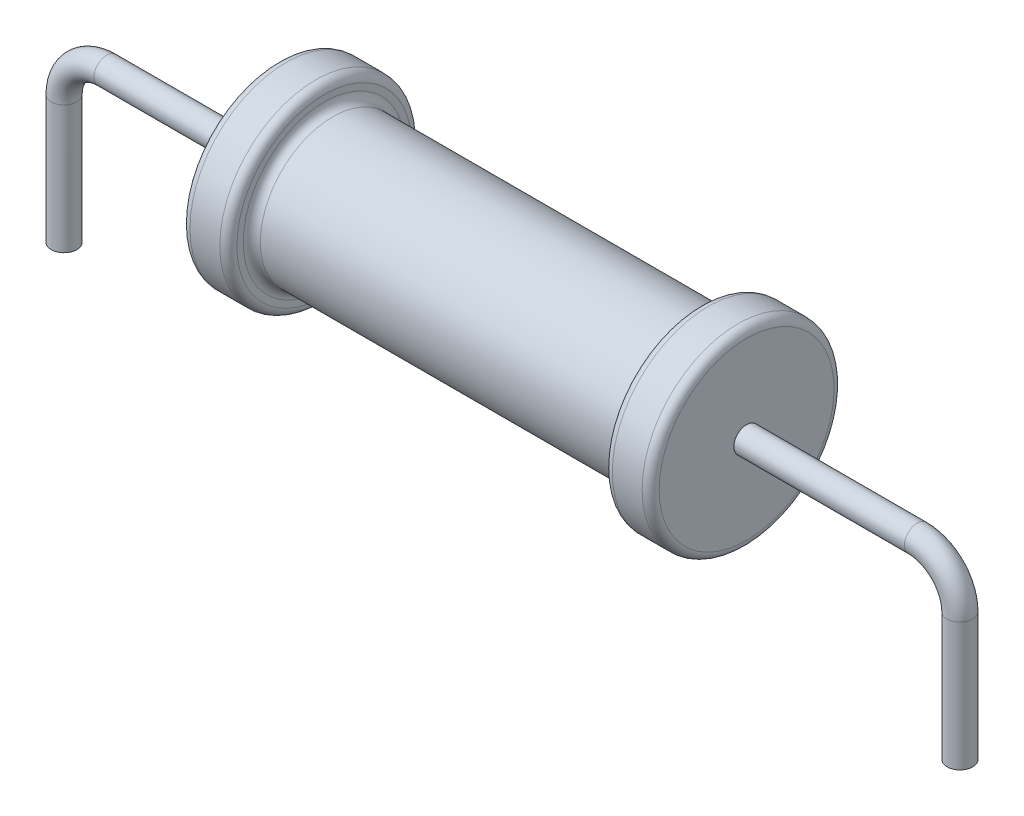
SolidWorks part; units mm, degrees
ref_plane "Спереди" through (0, 0, 0) normal (0, 0, 1) x (1, 0, 0)
ref_plane "Сверху" through (0, 0, 0) normal (0, 1, 0) x (1, 0, 0)
ref_plane "Справа" through (0, 0, 0) normal (1, 0, 0) x (0, 0, -1)
sketch "Эскиз2" plane through (0, 0, 0) normal (0, 1, 0) x (1, 0, 0)
  line L0 (-5.422, 0) -> (5.578, 0)
  line L1 (5.578, 0) -> (5.578, 2.05)
  line L2 (5.378, 2.25) -> (4.678, 2.25)
  line L3 (4.478, 2.05) -> (4.478, 1.9)
  line L4 (4.278, 1.7) -> (-4.122, 1.7)
  line L5 (-4.322, 1.9) -> (-4.322, 2.05)
  line L6 (-4.522, 2.25) -> (-5.222, 2.25)
  line L7 (-5.422, 2.05) -> (-5.422, 0)
  arc A0 (-5.222, 2.25) -> (-5.422, 2.05) centre (-5.222, 2.05) ccw
  arc A1 (4.278, 1.7) -> (4.478, 1.9) centre (4.278, 1.9) ccw
  arc A2 (5.578, 2.05) -> (5.378, 2.25) centre (5.378, 2.05) ccw
  arc A3 (4.678, 2.25) -> (4.478, 2.05) centre (4.678, 2.05) ccw
  arc A4 (-4.322, 1.9) -> (-4.122, 1.7) centre (-4.122, 1.9) ccw
  arc A5 (-4.322, 2.05) -> (-4.522, 2.25) centre (-4.522, 2.05) ccw
  point P11 (-5.422, 2.25)
  point P14 (4.478, 1.7)
  point P17 (5.578, 2.25)
  point P20 (4.478, 2.25)
  point P23 (-4.322, 1.7)
  point P26 (-4.322, 2.25)
  dimension "D7" = 0.2
  dimension "D8" = 0.2
  dimension "D1" = 11
  dimension "D2" = 1.1
  dimension "D3" = 1.1
  dimension "D4" = 0.55
  dimension "D5" = 0.55
  dimension "D6" = 2.25
revolve "Повернуть7" add sketch "Эскиз2" angle 360 about L0
sketch "Эскиз47" plane through (0, 0, 0) normal (0, 0, 1) x (1, 0, 0)
  line L0 (-5.422, 0) -> (-9.422, 0)
  line L1 (-5.422, 2.05) -> (-5.422, -2.05) construction
  line L2 (-10.422, -1) -> (-10.422, -4)
  arc A1 (-9.422, 0) -> (-10.422, -1) centre (-9.422, -1) ccw
  point P16 (-10.422, 0)
  dimension "D1" = 4
  dimension "D2" = 5
sweep "По траектории4" add path "Эскиз47" circular profile diameter 0.6 parameters "D3"=0.6
sketch "Эскиз92" plane through (0, 0, 0) normal (0, 0, 1) x (1, 0, 0)
  line L0 (5.578, 0) -> (9.578, 0)
  line L1 (5.578, -2.05) -> (5.578, 2.05) construction
  line L2 (10.578, -1) -> (10.578, -4)
  arc A0 (10.578, -1) -> (9.578, 0) centre (9.578, -1) ccw
  point P8 (10.578, 0)
  dimension "D3" = 1
  dimension "D1" = 5
  dimension "D2" = 4
sweep "По траектории5" add path "Эскиз92" circular profile diameter 0.6 parameters "D3"=0.6
equation "\"H\" = 11"
equation "\"H_05\" = \"H\" / 2"
equation "\"R\" = 4.5 / 2"
equation "\"Border\"= \"H\" / 10"
equation "\"BorderH\"= \"Border\" / 2"
equation "\"D1@Эскиз2\"=\"H\""
equation "\"D2@Эскиз2\"=\"Border\""
equation "\"D3@Эскиз2\"=\"Border\""
equation "\"D4@Эскиз2\"=\"BorderH\""
equation "\"D5@Эскиз2\"=\"BorderH\""
equation "\"D6@Эскиз2\"=\"R\""
equation "\"Leglen\"= 5"
equation "\"D2@Эскиз47\"=\"Leglen\""
equation "\"D1@Эскиз92\"=\"Leglen\""
